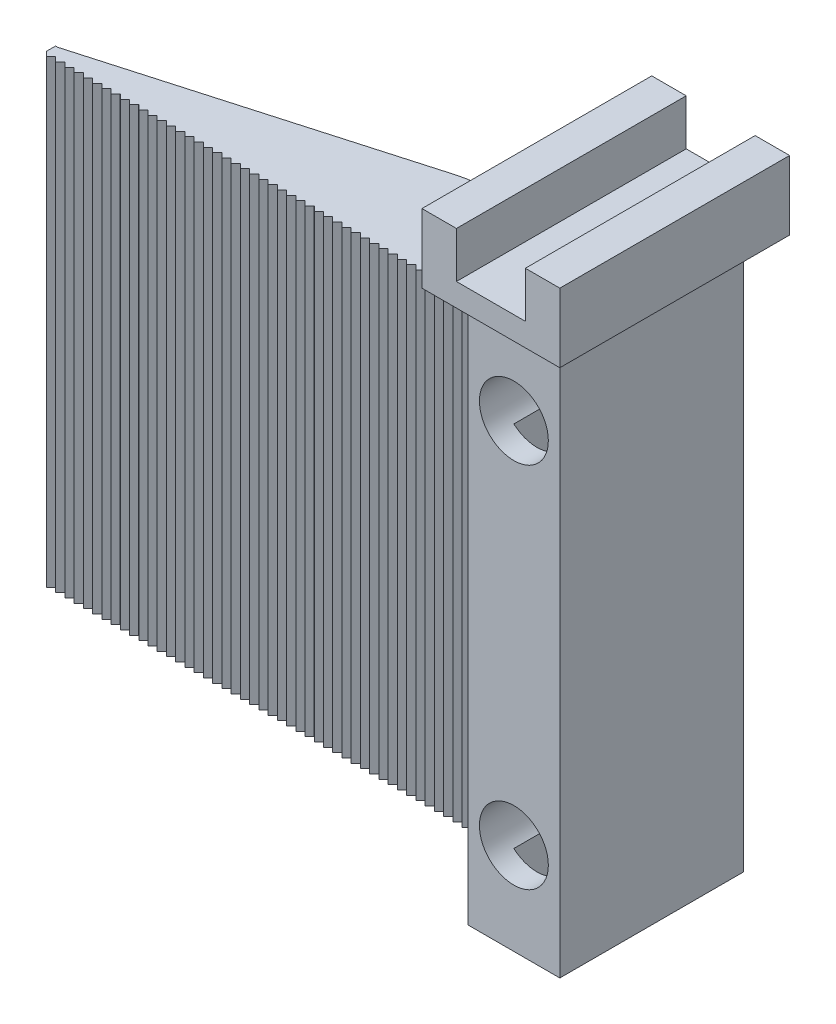
SolidWorks part; units mm, degrees
ref_plane "Front Plane" through (0, 0, 0) normal (0, 0, 1) x (1, 0, 0)
ref_plane "Top Plane" through (0, 0, 0) normal (0, 1, 0) x (1, 0, 0)
ref_plane "Right Plane" through (0, 0, 0) normal (1, 0, 0) x (0, 0, -1)
sketch "Sketch3" plane through (0, 0, 0) normal (0, 1, 0) x (1, 0, 0)
  line L0 (0, 0) -> (100, 0)
  line L1 (-55, 0) -> (55, 0) construction
  line L2 (100, 0) -> (100, 20)
  line L3 (100, 20) -> (70, 20)
  line L4 (70, 20) -> (0, 0)
  dimension "D1" = 100
  dimension "D2" = 20
  dimension "D3" = 30
extrude "Boss-Extrude1" add sketch "Sketch3" along normal blind 100
fillet "Fillet1" radius 20 1 edges at (70, 50, -20)
sketch "Sketch5" plane through (100, 0, 0) normal (1, 0, 0) x (0, 0, -1)
  line L0 (-10.7695, 110) -> (29.2305, 110)
  line L2 (29.2305, 110) -> (29.2305, -10)
  line L3 (29.2305, -10) -> (-10.7695, -10)
  line L4 (-10.7695, -10) -> (-10.7695, 110)
  dimension "D3" = 120
  dimension "D4" = 40
  dimension "D5" = 120
extrude "Boss-Extrude2" add sketch "Sketch5" along normal blind 20
sketch "Sketch6" plane through (0, 110, 0) normal (0, 1, 0) x (1, 0, 0)
  line L5 (105, 24.2305) -> (105, -5.7695)
  line L9 (115, -5.7695) -> (105, -5.7695)
  line L10 (115, -5.7695) -> (115, 24.2305)
  line L11 (115, 24.2305) -> (105, 24.2305)
  dimension "D1" = 30
  dimension "D2" = 10
extrude "Cut-Extrude1" cut sketch "Sketch6" against normal blind 120
sketch "Sketch7" plane through (0, 0, 0) normal (0, 0, 1) x (1, 0, 0)
  line L1 (100, 100) -> (0, 100)
  line L2 (100, 100) -> (100, 0)
  line L3 (100, 0) -> (0, 0)
  line L4 (0, 100) -> (0, 0)
extrude "Boss-Extrude3" add sketch "Sketch7" along normal blind 2
sketch "Sketch10" plane through (0, 100, 0) normal (0, 1, 0) x (1, 0, 0)
  line L0 (100, -2) -> (98, -2)
  line L1 (100, -2) -> (0, -2) construction
  line L2 (100, -2) -> (99, -3)
  line L3 (98, -2) -> (99, -3)
  line L4 (95.99, -2) -> (96.99, -3)
  line L5 (97.99, -2) -> (95.99, -2)
  line L6 (97.99, -2) -> (96.99, -3)
  line L7 (93.98, -2) -> (94.98, -3)
  line L8 (95.98, -2) -> (93.98, -2)
  line L9 (95.98, -2) -> (94.98, -3)
  line L10 (91.97, -2) -> (92.97, -3)
  line L11 (93.97, -2) -> (91.97, -2)
  line L12 (93.97, -2) -> (92.97, -3)
  line L13 (89.96, -2) -> (90.96, -3)
  line L14 (91.96, -2) -> (89.96, -2)
  line L15 (91.96, -2) -> (90.96, -3)
  line L16 (87.95, -2) -> (88.95, -3)
  line L17 (89.95, -2) -> (87.95, -2)
  line L18 (89.95, -2) -> (88.95, -3)
  line L19 (85.94, -2) -> (86.94, -3)
  line L20 (87.94, -2) -> (85.94, -2)
  line L21 (87.94, -2) -> (86.94, -3)
  line L22 (83.93, -2) -> (84.93, -3)
  line L23 (85.93, -2) -> (83.93, -2)
  line L24 (85.93, -2) -> (84.93, -3)
  line L25 (81.92, -2) -> (82.92, -3)
  line L26 (83.92, -2) -> (81.92, -2)
  line L27 (83.92, -2) -> (82.92, -3)
  line L28 (79.91, -2) -> (80.91, -3)
  line L29 (81.91, -2) -> (79.91, -2)
  line L30 (81.91, -2) -> (80.91, -3)
  line L31 (77.9, -2) -> (78.9, -3)
  line L32 (79.9, -2) -> (77.9, -2)
  line L33 (79.9, -2) -> (78.9, -3)
  line L34 (75.89, -2) -> (76.89, -3)
  line L35 (77.89, -2) -> (75.89, -2)
  line L36 (77.89, -2) -> (76.89, -3)
  line L37 (73.88, -2) -> (74.88, -3)
  line L38 (75.88, -2) -> (73.88, -2)
  line L39 (75.88, -2) -> (74.88, -3)
  line L40 (71.87, -2) -> (72.87, -3)
  line L41 (73.87, -2) -> (71.87, -2)
  line L42 (73.87, -2) -> (72.87, -3)
  line L43 (69.86, -2) -> (70.86, -3)
  line L44 (71.86, -2) -> (69.86, -2)
  line L45 (71.86, -2) -> (70.86, -3)
  line L46 (67.85, -2) -> (68.85, -3)
  line L47 (69.85, -2) -> (67.85, -2)
  line L48 (69.85, -2) -> (68.85, -3)
  line L49 (65.84, -2) -> (66.84, -3)
  line L50 (67.84, -2) -> (65.84, -2)
  line L51 (67.84, -2) -> (66.84, -3)
  line L52 (63.83, -2) -> (64.83, -3)
  line L53 (65.83, -2) -> (63.83, -2)
  line L54 (65.83, -2) -> (64.83, -3)
  line L55 (61.82, -2) -> (62.82, -3)
  line L56 (63.82, -2) -> (61.82, -2)
  line L57 (63.82, -2) -> (62.82, -3)
  line L58 (59.81, -2) -> (60.81, -3)
  line L59 (61.81, -2) -> (59.81, -2)
  line L60 (61.81, -2) -> (60.81, -3)
  line L61 (57.8, -2) -> (58.8, -3)
  line L62 (59.8, -2) -> (57.8, -2)
  line L63 (59.8, -2) -> (58.8, -3)
  line L64 (55.79, -2) -> (56.79, -3)
  line L65 (57.79, -2) -> (55.79, -2)
  line L66 (57.79, -2) -> (56.79, -3)
  line L67 (53.78, -2) -> (54.78, -3)
  line L68 (55.78, -2) -> (53.78, -2)
  line L69 (55.78, -2) -> (54.78, -3)
  line L70 (51.77, -2) -> (52.77, -3)
  line L71 (53.77, -2) -> (51.77, -2)
  line L72 (53.77, -2) -> (52.77, -3)
  line L73 (49.76, -2) -> (50.76, -3)
  line L74 (51.76, -2) -> (49.76, -2)
  line L75 (51.76, -2) -> (50.76, -3)
  line L76 (47.75, -2) -> (48.75, -3)
  line L77 (49.75, -2) -> (47.75, -2)
  line L78 (49.75, -2) -> (48.75, -3)
  line L79 (45.74, -2) -> (46.74, -3)
  line L80 (47.74, -2) -> (45.74, -2)
  line L81 (47.74, -2) -> (46.74, -3)
  line L82 (43.73, -2) -> (44.73, -3)
  line L83 (45.73, -2) -> (43.73, -2)
  line L84 (45.73, -2) -> (44.73, -3)
  line L85 (41.72, -2) -> (42.72, -3)
  line L86 (43.72, -2) -> (41.72, -2)
  line L87 (43.72, -2) -> (42.72, -3)
  line L88 (39.71, -2) -> (40.71, -3)
  line L89 (41.71, -2) -> (39.71, -2)
  line L90 (41.71, -2) -> (40.71, -3)
  line L91 (37.7, -2) -> (38.7, -3)
  line L92 (39.7, -2) -> (37.7, -2)
  line L93 (39.7, -2) -> (38.7, -3)
  line L94 (35.69, -2) -> (36.69, -3)
  line L95 (37.69, -2) -> (35.69, -2)
  line L96 (37.69, -2) -> (36.69, -3)
  line L97 (33.68, -2) -> (34.68, -3)
  line L98 (35.68, -2) -> (33.68, -2)
  line L99 (35.68, -2) -> (34.68, -3)
  line L100 (31.67, -2) -> (32.67, -3)
  line L101 (33.67, -2) -> (31.67, -2)
  line L102 (33.67, -2) -> (32.67, -3)
  line L103 (29.66, -2) -> (30.66, -3)
  line L104 (31.66, -2) -> (29.66, -2)
  line L105 (31.66, -2) -> (30.66, -3)
  line L106 (27.65, -2) -> (28.65, -3)
  line L107 (29.65, -2) -> (27.65, -2)
  line L108 (29.65, -2) -> (28.65, -3)
  line L109 (25.64, -2) -> (26.64, -3)
  line L110 (27.64, -2) -> (25.64, -2)
  line L111 (27.64, -2) -> (26.64, -3)
  line L112 (23.63, -2) -> (24.63, -3)
  line L113 (25.63, -2) -> (23.63, -2)
  line L114 (25.63, -2) -> (24.63, -3)
  line L115 (21.62, -2) -> (22.62, -3)
  line L116 (23.62, -2) -> (21.62, -2)
  line L117 (23.62, -2) -> (22.62, -3)
  line L118 (19.61, -2) -> (20.61, -3)
  line L119 (21.61, -2) -> (19.61, -2)
  line L120 (21.61, -2) -> (20.61, -3)
  line L121 (17.6, -2) -> (18.6, -3)
  line L122 (19.6, -2) -> (17.6, -2)
  line L123 (19.6, -2) -> (18.6, -3)
  line L124 (15.59, -2) -> (16.59, -3)
  line L125 (17.59, -2) -> (15.59, -2)
  line L126 (17.59, -2) -> (16.59, -3)
  line L127 (13.58, -2) -> (14.58, -3)
  line L128 (15.58, -2) -> (13.58, -2)
  line L129 (15.58, -2) -> (14.58, -3)
  line L130 (11.57, -2) -> (12.57, -3)
  line L131 (13.57, -2) -> (11.57, -2)
  line L132 (13.57, -2) -> (12.57, -3)
  line L133 (9.56, -2) -> (10.56, -3)
  line L134 (11.56, -2) -> (9.56, -2)
  line L135 (11.56, -2) -> (10.56, -3)
  line L136 (7.55, -2) -> (8.55, -3)
  line L137 (9.55, -2) -> (7.55, -2)
  line L138 (9.55, -2) -> (8.55, -3)
  line L139 (5.54, -2) -> (6.54, -3)
  line L140 (7.54, -2) -> (5.54, -2)
  line L141 (7.54, -2) -> (6.54, -3)
  line L142 (3.53, -2) -> (4.53, -3)
  line L143 (5.53, -2) -> (3.53, -2)
  line L144 (5.53, -2) -> (4.53, -3)
  line L145 (1.52, -2) -> (2.52, -3)
  line L146 (3.52, -2) -> (1.52, -2)
  line L147 (3.52, -2) -> (2.52, -3)
  line L148 (-0.49, -2) -> (0.51, -3)
  line L149 (1.51, -2) -> (-0.49, -2)
  line L150 (1.51, -2) -> (0.51, -3)
  dimension "D1" = 2
  dimension "D2" = 1.4142
  dimension "D3" = 50
extrude "Boss-Extrude4" add sketch "Sketch10" against normal blind 100
sketch "Sketch11" plane through (0, 100, 0) normal (0, 1, 0) x (1, 0, 0)
  line L0 (-0.49, -2) -> (0, -2)
  line L1 (0, -22) -> (0, 22) construction
  line L2 (0, -2) -> (-0.49, -2) construction
  line L3 (0, -2) -> (0, 0)
  line L4 (-0.49, -2) -> (-0.49, 0)
  line L5 (-66, 0) -> (66, 0) construction
  line L6 (-0.49, 0) -> (0, 0)
extrude "Boss-Extrude5" add sketch "Sketch11" against normal blind 100
sketch "Sketch12" plane through (0, 0, 10.7695) normal (0, 0, 1) x (1, 0, 0)
  circle A0 centre (110, 10) radius 7.5
  circle A1 centre (110, 90) radius 7.5
  dimension "D3" = 15
  dimension "D4" = 15
extrude "Cut-Extrude2" cut sketch "Sketch12" against normal blind 40
sketch "Sketch15" plane through (0, 110, 0) normal (0, 1, 0) x (1, 0, 0)
  line L3 (95, 34.2305) -> (125, 34.2305)
  line L4 (125, 34.2305) -> (125, -15.7695)
  line L5 (125, -15.7695) -> (95, -15.7695)
  line L6 (95, -15.7695) -> (95, 34.2305)
  dimension "D3" = 30
  dimension "D4" = 50
extrude "Boss-Extrude6" add sketch "Sketch15" along normal blind 15
sketch "Sketch16" plane through (0, 125, 0) normal (0, 1, 0) x (1, 0, 0)
  line L0 (95, 34.2305) -> (95, -15.7695) construction
  line L1 (125, 34.2305) -> (95, 34.2305) construction
  line L2 (102.5, 34.2305) -> (102.5, -15.7695)
  line L3 (95, -15.7695) -> (125, -15.7695) construction
  line L4 (102.5, -15.7695) -> (117.5, -15.7695)
  line L5 (117.5, -15.7695) -> (117.5, 34.2305)
  line L6 (117.5, 34.2305) -> (102.5, 34.2305)
  dimension "D1" = 7.5
  dimension "D2" = 15
extrude "Cut-Extrude3" cut sketch "Sketch16" against normal blind 10
